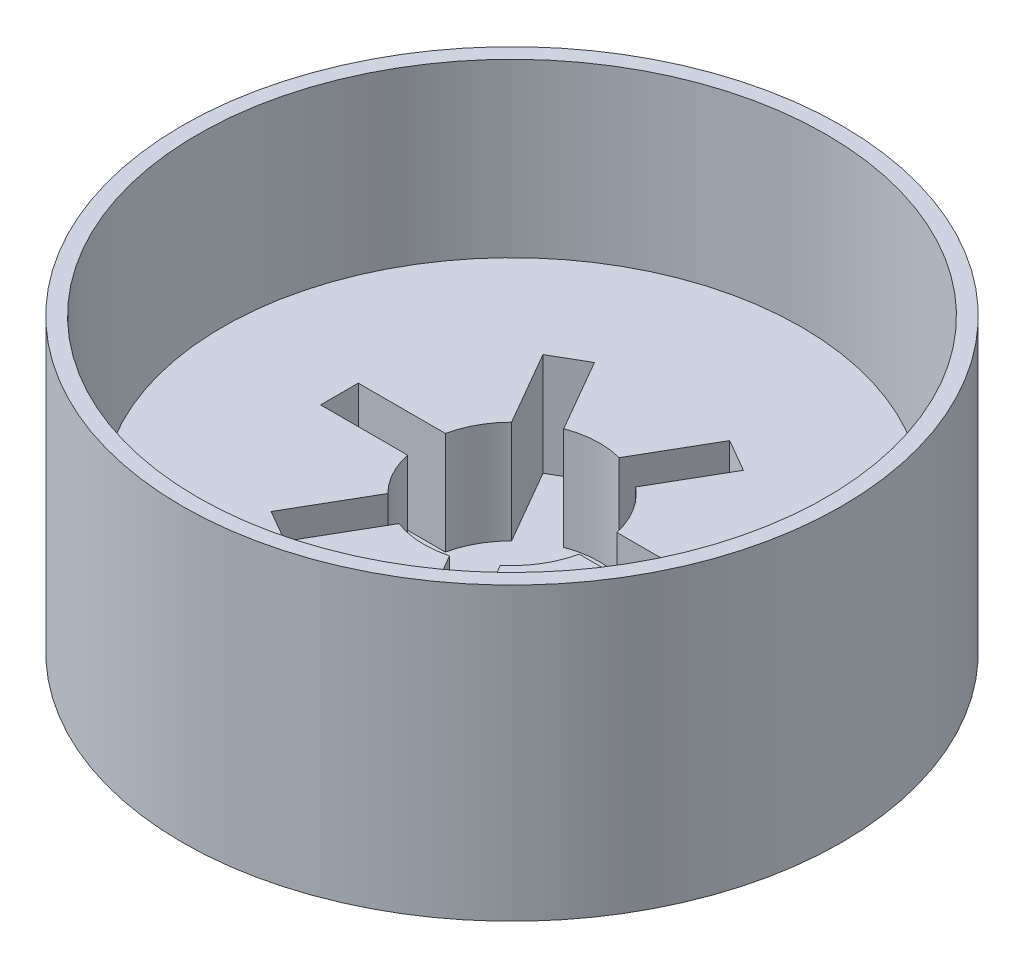
SolidWorks part; units mm, degrees
ref_plane "Front" through (0, 0, 0) normal (0, 0, 1) x (1, 0, 0)
ref_plane "Top" through (0, 0, 0) normal (0, 1, 0) x (1, 0, 0)
ref_plane "Right" through (0, 0, 0) normal (1, 0, 0) x (0, 0, -1)
sketch "Sketch3" plane through (0, 0, 0) normal (0, 1, 0) x (1, 0, 0)
  circle A0 centre (0, 0) radius 48.895
  dimension "D1" = 97.79
extrude "Boss-Extrude2" add sketch "Sketch3" along normal blind 5.08
sketch "Sketch4" plane through (0, 5.08, 0) normal (0, 1, 0) x (1, 0, 0)
  line L18 (-4.5374, 12.2107) -> (-10.7587, 22.9863)
  line L19 (-10.7587, 22.9863) -> (-15.598, 20.1923)
  line L20 (-12.7162, 2.8262) -> (-25.6243, 2.8262)
  line L21 (-12.7303, -2.7618) -> (-25.6243, -2.7618)
  line L22 (-25.6243, 2.8262) -> (-25.6243, -2.7618)
  line L23 (-9.2408, 9.1813) -> (-15.598, 20.1923)
  line L24 (8.2809, 10.0556) -> (14.1333, 20.1923)
  line L25 (14.1333, 20.1923) -> (9.294, 22.9863)
  line L26 (3.2986, 12.6019) -> (9.294, 22.9863)
  line L27 (12.7303, -2.7618) -> (24.1597, -2.7618)
  line L28 (24.1597, -2.7618) -> (24.1597, 2.8262)
  line L29 (12.7162, 2.8262) -> (24.1597, 2.8262)
  line L30 (3.3308, -12.5934) -> (9.294, -22.922)
  line L31 (9.294, -22.922) -> (14.1333, -20.128)
  line L32 (8.3061, -10.0348) -> (14.1333, -20.128)
  line L33 (-9.2643, -9.1576) -> (-15.598, -20.128)
  line L34 (-15.598, -20.128) -> (-10.7587, -22.922)
  line L35 (-4.5679, -12.1993) -> (-10.7587, -22.922)
  arc A7 (-12.7303, -2.7618) -> (-9.2643, -9.1576) centre (0, 0) ccw
  arc A8 (-9.2408, 9.1813) -> (-12.7162, 2.8262) centre (0, 0) ccw
  arc A9 (3.2986, 12.6019) -> (-4.5374, 12.2107) centre (0, 0) ccw
  arc A10 (12.7162, 2.8262) -> (8.2809, 10.0556) centre (0, 0) ccw
  arc A11 (8.3061, -10.0348) -> (12.7303, -2.7618) centre (0, 0) ccw
  arc A12 (-4.5679, -12.1993) -> (3.3308, -12.5934) centre (0, 0) ccw
  circle A13 centre (0, 0) radius 42.9006
  point P56 (0, 0)
  dimension "D1" = 85.8012
extrude "Boss-Extrude3" add sketch "Sketch4" along normal blind 15.24 contours A13 A12 L35 L34 L33 A7 L21 L22 L20 A8 L23 L19 L18 A9 L26 L25 L24 A10 L29 L28 L27 A11 L32 L31 L30
sketch "Sketch5" plane through (0, 5.08, 0) normal (0, 1, 0) x (1, 0, 0)
  circle A0 centre (0, 0) radius 46.609
  circle A1 centre (0, 0) radius 48.895
  circle A2 centre (0, 0) radius 48.895 construction
  dimension "D1" = 93.218
extrude "Boss-Extrude4" add sketch "Sketch5" along normal blind 38.1
sketch "Sketch7" plane through (0, 0, 0) normal (0, -1, 0) x (1, 0, 0)
  line L0 (10.1891, 28.7771) -> (3.9055, 28.7771)
  line L1 (3.4451, -11.1863) -> (4.1309, -8.9003)
  line L2 (4.1309, -8.9003) -> (3.845, -8.832)
  line L3 (1.5782, -8.2907) -> (0.9354, -10.4334)
  line L4 (2.0723, -8.4087) -> (1.5782, -8.2907)
  spline S0 degree 2 poles (3.4451, -11.1863) (6.5133, -11.3926) (9.2949, -9.7629) knots 0 0 0 1 1 1
  spline S1 degree 2 poles (3.2578, -15.1876) (7.2446, -13.6144) (9.2949, -9.7629) knots 0 0 0 1 1 1
  spline S2 degree 2 poles (-3.9217, -32.2612) (0.677, -24.1574) (3.2578, -15.1876) knots 0 0 0 1 1 1
  spline S3 degree 2 poles (-5.4963, -32.1522) (-5.134, -22.7162) (-1.5351, -14.0461) knots 0 0 0 1 1 1
  spline S4 degree 2 poles (-3.9217, -32.2612) (-5.5914, -34.7217) (-5.4963, -32.1522) knots 0 0 0 1 1 1
  spline S5 degree 2 poles (-1.5351, -14.0461) (-3.9978, -10.5124) (-2.6484, -6.465) knots 0 0 0 1 1 1
  spline S6 degree 2 poles (0.9354, -10.4334) (-1.7307, -9.2479) (-2.6484, -6.465) knots 0 0 0 1 1 1
  spline S7 degree 2 poles (10.1891, 28.7771) (10.4945, 9.2911) (3.845, -8.832) knots 0 0 0 1 1 1
  spline S8 degree 2 poles (3.9055, 28.7771) (5.6734, 10.0822) (2.0723, -8.4087) knots 0 0 0 1 1 1
  point P22 (4.4415, 13.0372)
extrude "Cut-Extrude1" cut sketch "Sketch7" against normal blind 0.2
